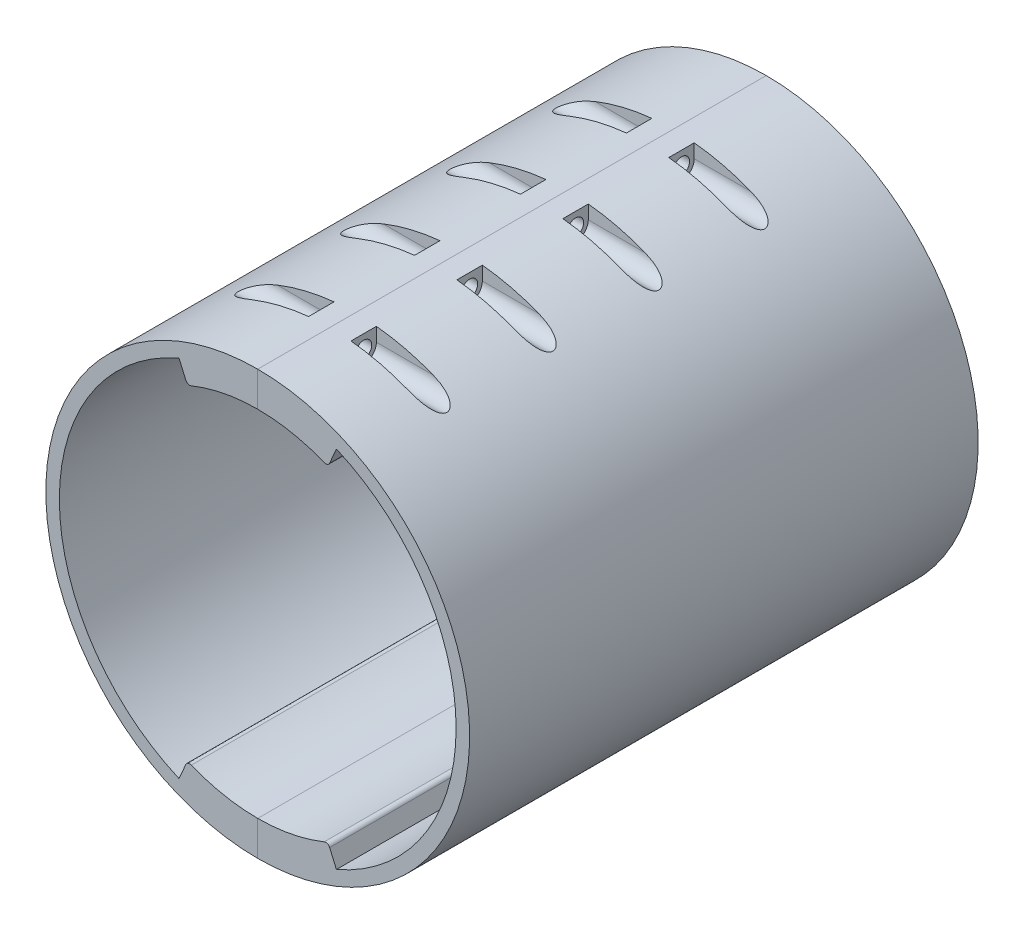
SolidWorks part; units mm, degrees
material "ABS"
ref_plane "Front Plane" through (0, 0, 0) normal (0, 0, 1) x (1, 0, 0)
ref_plane "Top Plane" through (0, 0, 0) normal (0, 1, 0) x (1, 0, 0)
ref_plane "Right Plane" through (0, 0, 0) normal (1, 0, 0) x (0, 0, -1)
sketch "Sketch1" plane through (0, 0, 0) normal (0, 1, 0) x (1, 0, 0)
  line L1 (0, 0) -> (-300, 0)
  line L2 (0, 0) -> (0, -170)
  line L3 (0, -170) -> (-300, -170)
  line L4 (-300, 0) -> (-300, -170)
  dimension "D1" = 300
  dimension "D2" = 170
extrude "Boss-Extrude1" add sketch "Sketch1" along normal blind 225
shell "Shell1" thickness 10
sketch "Sketch2" plane through (0, 0, 10) normal (0, 0, 1) x (1, 0, 0)
  line L0 (-290, 112.5) -> (-10, 112.5) construction
  line L1 (-290, 215) -> (-290, 10) construction
  line L2 (-10, 215) -> (-10, 10) construction
  circle A0 centre (-150, 112.5) radius 6.5
  dimension "D1" = 13
  dimension "D2" = 140
extrude "Cut-Extrude1" cut sketch "Sketch2" against normal blind 10
sketch "Sketch3" plane through (0, 0, 10) normal (0, 0, 1) x (1, 0, 0)
  line L0 (-150, 112.5) -> (-150, 135) construction
  line L1 (-150, 112.5) -> (-134.0901, 128.4099) construction
  circle A0 centre (-150, 112.5) radius 22.5 construction
  dimension "D1" = 45
  dimension "D2" = 45
hole_wizard "M5 Clearance Hole1" positions "Sketch4" profile "Sketch5" hole size "M5" standard "ANSI Metric"
sketch "Sketch4" plane through (0, 0, 10) normal (0, 0, 1) x (1, 0, 0)
  point P0 (-134.0901, 128.4099)
sketch "Sketch5" plane through (-134.0901, 128.4099, 10) normal (1, 0, 0) x (0, -1, 0)
  line L0 (0, 0) -> (0, 21.6524)
  line L1 (0, 21.6524) -> (2.75, 20)
  line L2 (2.75, 20) -> (2.75, 0.025)
  line L3 (2.75, 0.025) -> (2.775, 0)
  line L5 (2.775, 0) -> (0, 0)
  line L6 (-2.75, 0.025) -> (-2.775, 0) construction
  line L10 (0, 21.6524) -> (-2.75, 20) construction
  line L11 (0, -6.35) -> (0, 107.95) construction
  dimension "Hole Dia." = 5.5
  dimension "Hole Depth" = 20
  dimension "Near C'Sink Dia." = 5.55
  dimension "Near C'Sink Angle" = 90
  dimension "Drill Angle" = 118
pattern_circular "CirPattern1" count 4 over 360 about axis through (-150, 112.5, 0) along (0, 0, 1) of "M5 Clearance Hole1"
sketch "Sketch6" plane through (0, 0, 0) normal (0, 0, -1) x (-1, 0, 0)
  circle A0 centre (150, 112.5) radius 100
  dimension "D1" = 200
extrude "Cut-Extrude2" cut sketch "Sketch6" against normal through all flip side to cut
sketch "Sketch7" plane through (0, 0, 10) normal (0, 0, 1) x (1, 0, 0)
  circle A0 centre (-150, 112.5) radius 93.619
  circle A2 centre (-150, 112.5) radius 100
  dimension "D1" = 6.381
extrude "Boss-Extrude2" add sketch "Sketch7" along normal blind 200
sketch "Sketch8" plane through (0, 0, 0) normal (0, 0, -1) x (-1, 0, 0)
  circle A0 centre (150, 112.5) radius 95
  circle A1 centre (150, 112.5) radius 100
  circle A2 centre (150, 112.5) radius 100 construction
  dimension "D1" = 5
extrude "Boss-Extrude3" add sketch "Sketch8" along normal blind 30
ref_plane "Plane1" through (-50, 0, 0) normal (1, 0, 0) x (0, 0, -1)
ref_plane "Plane2" through (-150, 0, 0) normal (1, 0, 0) x (0, 0, -1)
sketch "Sketch11" plane through (0, 0, 0) normal (0, 0, -1) x (-1, 0, 0)
  circle A0 centre (150, 112.5) radius 90
  circle A1 centre (150, 112.5) radius 95
  circle A2 centre (150, 112.5) radius 95 construction
  dimension "D1" = 180
extrude "Boss-Extrude4" add sketch "Sketch11" along normal up to surface (30 mm away) up to face at (-250, 112.5, -30)
sketch "Sketch12" plane through (-150, 0, 0) normal (1, 0, 0) x (0, 0, -1)
  line L0 (-170, 205.5) -> (30, 205.5) construction
  line L1 (30, 12.5) -> (30, 212.5) construction
  line L2 (-210, 212.5) -> (-210, 12.5) construction
  line L3 (30, 212.5) -> (-210, 212.5) construction
  line L4 (-176, 205.5) -> (-176, 212.5)
  line L5 (-164, 205.5) -> (-164, 212.5)
  line L6 (-164, 212.5) -> (-176, 212.5)
  line L7 (-126, 205.5) -> (-126, 212.5)
  line L8 (-114, 212.5) -> (-126, 212.5)
  line L9 (-114, 205.5) -> (-114, 212.5)
  line L10 (-76, 205.5) -> (-76, 212.5)
  line L11 (-64, 212.5) -> (-76, 212.5)
  line L12 (-64, 205.5) -> (-64, 212.5)
  line L13 (-26, 205.5) -> (-26, 212.5)
  line L14 (-14, 212.5) -> (-26, 212.5)
  line L15 (-14, 205.5) -> (-14, 212.5)
  line L16 (-210, 112.5) -> (30, 112.5) construction
  line L17 (-170, 19.5) -> (30, 19.5) construction
  line L18 (-14, 19.5) -> (-14, 12.5)
  line L19 (-14, 12.5) -> (-26, 12.5)
  line L20 (-26, 19.5) -> (-26, 12.5)
  line L21 (-64, 19.5) -> (-64, 12.5)
  line L22 (-64, 12.5) -> (-76, 12.5)
  line L23 (-76, 19.5) -> (-76, 12.5)
  line L24 (-114, 19.5) -> (-114, 12.5)
  line L25 (-114, 12.5) -> (-126, 12.5)
  line L26 (-126, 19.5) -> (-126, 12.5)
  line L27 (-164, 12.5) -> (-176, 12.5)
  line L28 (-164, 19.5) -> (-164, 12.5)
  line L29 (-176, 19.5) -> (-176, 12.5)
  arc A0 (-176, 205.5) -> (-164, 205.5) centre (-170, 205.5) ccw
  arc A1 (-126, 205.5) -> (-114, 205.5) centre (-120, 205.5) ccw
  arc A2 (-76, 205.5) -> (-64, 205.5) centre (-70, 205.5) ccw
  arc A3 (-26, 205.5) -> (-14, 205.5) centre (-20, 205.5) ccw
  arc A4 (-26, 19.5) -> (-14, 19.5) centre (-20, 19.5) cw
  arc A5 (-76, 19.5) -> (-64, 19.5) centre (-70, 19.5) cw
  arc A6 (-126, 19.5) -> (-114, 19.5) centre (-120, 19.5) cw
  arc A7 (-176, 19.5) -> (-164, 19.5) centre (-170, 19.5) cw
  dimension "D2" = 12
  dimension "D1" = 40
  dimension "D3" = 7
  dimension "D4" = 4
ref_plane "Plane3" through (-140, 0, 0) normal (1, 0, 0) x (0, 0, -1)
sketch "Sketch13" plane through (-140, 0, 0) normal (1, 0, 0) x (0, 0, -1)
  line L3 (-176, 212.5) -> (-176, 205.5)
  line L4 (-164, 212.5) -> (-176, 212.5)
  line L5 (-164, 205.5) -> (-164, 212.5)
  line L6 (-176, 212.5) -> (-176, 205.5)
  line L7 (-164, 212.5) -> (-176, 212.5)
  line L8 (-164, 205.5) -> (-164, 212.5)
  line L9 (-26, 212.5) -> (-26, 205.5)
  line L10 (-14, 212.5) -> (-26, 212.5)
  line L11 (-14, 205.5) -> (-14, 212.5)
  line L12 (-26, 212.5) -> (-26, 205.5)
  line L13 (-14, 212.5) -> (-26, 212.5)
  line L14 (-14, 205.5) -> (-14, 212.5)
  line L15 (-76, 212.5) -> (-76, 205.5)
  line L16 (-64, 212.5) -> (-76, 212.5)
  line L17 (-64, 205.5) -> (-64, 212.5)
  line L18 (-76, 212.5) -> (-76, 205.5)
  line L19 (-64, 212.5) -> (-76, 212.5)
  line L20 (-64, 205.5) -> (-64, 212.5)
  line L21 (-114, 212.5) -> (-126, 212.5)
  line L22 (-114, 205.5) -> (-114, 212.5)
  line L23 (-126, 212.5) -> (-126, 205.5)
  line L24 (-114, 212.5) -> (-126, 212.5)
  line L25 (-114, 205.5) -> (-114, 212.5)
  line L26 (-126, 212.5) -> (-126, 205.5)
  line L27 (-114, 12.5) -> (-114, 19.5)
  line L28 (-126, 12.5) -> (-114, 12.5)
  line L29 (-126, 19.5) -> (-126, 12.5)
  line L30 (-114, 12.5) -> (-114, 19.5)
  line L31 (-126, 12.5) -> (-114, 12.5)
  line L32 (-126, 19.5) -> (-126, 12.5)
  line L33 (-64, 12.5) -> (-64, 19.5)
  line L34 (-76, 12.5) -> (-64, 12.5)
  line L35 (-76, 19.5) -> (-76, 12.5)
  line L36 (-64, 12.5) -> (-64, 19.5)
  line L37 (-76, 12.5) -> (-64, 12.5)
  line L38 (-76, 19.5) -> (-76, 12.5)
  line L39 (-14, 12.5) -> (-14, 19.5)
  line L40 (-26, 12.5) -> (-14, 12.5)
  line L41 (-26, 19.5) -> (-26, 12.5)
  line L42 (-14, 12.5) -> (-14, 19.5)
  line L43 (-26, 12.5) -> (-14, 12.5)
  line L44 (-26, 19.5) -> (-26, 12.5)
  line L45 (-176, 12.5) -> (-164, 12.5)
  line L46 (-176, 19.5) -> (-176, 12.5)
  line L47 (-164, 12.5) -> (-164, 19.5)
  line L48 (-176, 12.5) -> (-164, 12.5)
  line L49 (-176, 19.5) -> (-176, 12.5)
  line L50 (-164, 12.5) -> (-164, 19.5)
  arc A1 (-176, 205.5) -> (-164, 205.5) centre (-170, 205.5) ccw
  arc A2 (-176, 205.5) -> (-164, 205.5) centre (-170, 205.5) ccw
  arc A3 (-26, 205.5) -> (-14, 205.5) centre (-20, 205.5) ccw
  arc A4 (-26, 205.5) -> (-14, 205.5) centre (-20, 205.5) ccw
  arc A5 (-76, 205.5) -> (-64, 205.5) centre (-70, 205.5) ccw
  arc A6 (-76, 205.5) -> (-64, 205.5) centre (-70, 205.5) ccw
  arc A7 (-126, 205.5) -> (-114, 205.5) centre (-120, 205.5) ccw
  arc A8 (-126, 205.5) -> (-114, 205.5) centre (-120, 205.5) ccw
  arc A9 (-114, 19.5) -> (-126, 19.5) centre (-120, 19.5) ccw
  arc A10 (-114, 19.5) -> (-126, 19.5) centre (-120, 19.5) ccw
  arc A11 (-64, 19.5) -> (-76, 19.5) centre (-70, 19.5) ccw
  arc A12 (-64, 19.5) -> (-76, 19.5) centre (-70, 19.5) ccw
  arc A13 (-14, 19.5) -> (-26, 19.5) centre (-20, 19.5) ccw
  arc A14 (-14, 19.5) -> (-26, 19.5) centre (-20, 19.5) ccw
  arc A15 (-164, 19.5) -> (-176, 19.5) centre (-170, 19.5) ccw
  arc A16 (-164, 19.5) -> (-176, 19.5) centre (-170, 19.5) ccw
  dimension "D1" = 0
  dimension "D2" = 0
  dimension "D3" = 0
  dimension "D4" = 0
  dimension "D5" = 0
  dimension "D6" = 0
  dimension "D7" = 0
  dimension "D8" = 0
extrude "Cut-Extrude3" cut sketch "Sketch13" along normal blind 47
mirror "Mirror1" about plane through (-150, 0, 0) normal (1, 0, 0) of "Cut-Extrude3"
sketch "Sketch15" plane through (0, 0, 210) normal (0, 0, 1) x (1, 0, 0)
  line L0 (-150, 12.5) -> (-150, 212.5) construction
  line L1 (-187.1354, 198.4388) -> (-183.1688, 189.2592)
  line L2 (-112.8646, 198.4388) -> (-116.8312, 189.2592)
  line L3 (-150, 112.5) -> (-86.3141, 112.5) construction
  line L4 (-112.8646, 26.5612) -> (-116.8312, 35.7408)
  line L5 (-187.1354, 26.5612) -> (-183.1688, 35.7408)
  circle A0 centre (-150, 112.5) radius 100 construction
  arc A1 (-187.1354, 198.4388) -> (-112.8646, 198.4388) centre (-150, 112.5) cw
  circle A2 centre (-150, 112.5) radius 93.619 construction
  arc A3 (-183.1688, 189.2592) -> (-116.8312, 189.2592) centre (-150, 112.5) cw
  arc A4 (-183.1688, 35.7408) -> (-116.8312, 35.7408) centre (-150, 112.5) ccw
  arc A5 (-187.1354, 26.5612) -> (-112.8646, 26.5612) centre (-150, 112.5) ccw
  point P7 (-150, 112.5)
  dimension "D1" = 10
extrude "Boss-Extrude6" add sketch "Sketch15" against normal up to next
fillet "Fillet2" radius 2 4 edges at (-116.8312, 189.2592, 110) (-183.1688, 189.2592, 110) (-183.1688, 35.7408, 110) (-116.8312, 35.7408, 110)
sketch "Sketch16" plane through (-140, 0, 0) normal (1, 0, 0) x (0, 0, -1)
  line L3 (-76, 212.5) -> (-76, 205.5)
  line L4 (-64, 205.5) -> (-64, 212.5)
  line L5 (-64, 212.5) -> (-76, 212.5)
  line L6 (-76, 212.5) -> (-76, 205.5)
  line L7 (-64, 205.5) -> (-64, 212.5)
  line L8 (-64, 212.5) -> (-76, 212.5)
  line L9 (-26, 212.5) -> (-26, 205.5)
  line L10 (-14, 205.5) -> (-14, 212.5)
  line L11 (-14, 212.5) -> (-26, 212.5)
  line L12 (-26, 212.5) -> (-26, 205.5)
  line L13 (-14, 205.5) -> (-14, 212.5)
  line L14 (-14, 212.5) -> (-26, 212.5)
  line L15 (-176, 212.5) -> (-176, 205.5)
  line L16 (-164, 205.5) -> (-164, 212.5)
  line L17 (-164, 212.5) -> (-176, 212.5)
  line L18 (-176, 212.5) -> (-176, 205.5)
  line L19 (-164, 205.5) -> (-164, 212.5)
  line L20 (-164, 212.5) -> (-176, 212.5)
  line L21 (-64, 12.5) -> (-64, 19.5)
  line L22 (-76, 19.5) -> (-76, 12.5)
  line L23 (-76, 12.5) -> (-64, 12.5)
  line L24 (-64, 12.5) -> (-64, 19.5)
  line L25 (-76, 19.5) -> (-76, 12.5)
  line L26 (-76, 12.5) -> (-64, 12.5)
  line L27 (-114, 12.5) -> (-114, 19.5)
  line L28 (-126, 19.5) -> (-126, 12.5)
  line L29 (-126, 12.5) -> (-114, 12.5)
  line L30 (-114, 12.5) -> (-114, 19.5)
  line L31 (-126, 19.5) -> (-126, 12.5)
  line L32 (-126, 12.5) -> (-114, 12.5)
  line L33 (-114, 212.5) -> (-126, 212.5)
  line L34 (-114, 205.5) -> (-114, 212.5)
  line L35 (-126, 212.5) -> (-126, 205.5)
  line L36 (-114, 212.5) -> (-126, 212.5)
  line L37 (-114, 205.5) -> (-114, 212.5)
  line L38 (-126, 212.5) -> (-126, 205.5)
  line L39 (-176, 12.5) -> (-164, 12.5)
  line L40 (-164, 12.5) -> (-164, 19.5)
  line L41 (-176, 19.5) -> (-176, 12.5)
  line L42 (-176, 12.5) -> (-164, 12.5)
  line L43 (-164, 12.5) -> (-164, 19.5)
  line L44 (-176, 19.5) -> (-176, 12.5)
  line L45 (-26, 19.5) -> (-26, 12.5)
  line L46 (-14, 12.5) -> (-14, 19.5)
  line L47 (-26, 12.5) -> (-14, 12.5)
  line L48 (-26, 19.5) -> (-26, 12.5)
  line L49 (-14, 12.5) -> (-14, 19.5)
  line L50 (-26, 12.5) -> (-14, 12.5)
  arc A1 (-76, 205.5) -> (-64, 205.5) centre (-70, 205.5) ccw
  arc A2 (-76, 205.5) -> (-64, 205.5) centre (-70, 205.5) ccw
  arc A3 (-26, 205.5) -> (-14, 205.5) centre (-20, 205.5) ccw
  arc A4 (-26, 205.5) -> (-14, 205.5) centre (-20, 205.5) ccw
  arc A5 (-176, 205.5) -> (-164, 205.5) centre (-170, 205.5) ccw
  arc A6 (-176, 205.5) -> (-164, 205.5) centre (-170, 205.5) ccw
  arc A7 (-64, 19.5) -> (-76, 19.5) centre (-70, 19.5) ccw
  arc A8 (-64, 19.5) -> (-76, 19.5) centre (-70, 19.5) ccw
  arc A9 (-114, 19.5) -> (-126, 19.5) centre (-120, 19.5) ccw
  arc A10 (-114, 19.5) -> (-126, 19.5) centre (-120, 19.5) ccw
  arc A11 (-126, 205.5) -> (-114, 205.5) centre (-120, 205.5) ccw
  arc A12 (-126, 205.5) -> (-114, 205.5) centre (-120, 205.5) ccw
  arc A13 (-164, 19.5) -> (-176, 19.5) centre (-170, 19.5) ccw
  arc A14 (-164, 19.5) -> (-176, 19.5) centre (-170, 19.5) ccw
  arc A15 (-14, 19.5) -> (-26, 19.5) centre (-20, 19.5) ccw
  arc A16 (-14, 19.5) -> (-26, 19.5) centre (-20, 19.5) ccw
  dimension "D1" = 0
  dimension "D2" = 0
  dimension "D3" = 0
  dimension "D4" = 0
  dimension "D5" = 0
  dimension "D6" = 0
  dimension "D7" = 0
  dimension "D8" = 0
extrude "Cut-Extrude4" cut sketch "Sketch16" along normal blind 35
sketch "Sketch17" plane through (-160, 0, 0) normal (-1, 0, 0) x (0, 0, 1)
  line L3 (76, 205.5) -> (76, 212.5)
  line L4 (64, 212.5) -> (64, 205.5)
  line L5 (76, 212.5) -> (64, 212.5)
  line L6 (76, 205.5) -> (76, 212.5)
  line L7 (64, 212.5) -> (64, 205.5)
  line L8 (76, 212.5) -> (64, 212.5)
  line L9 (26, 205.5) -> (26, 212.5)
  line L10 (14, 212.5) -> (14, 205.5)
  line L11 (26, 212.5) -> (14, 212.5)
  line L12 (26, 205.5) -> (26, 212.5)
  line L13 (14, 212.5) -> (14, 205.5)
  line L14 (26, 212.5) -> (14, 212.5)
  line L15 (176, 205.5) -> (176, 212.5)
  line L16 (164, 212.5) -> (164, 205.5)
  line L17 (176, 212.5) -> (164, 212.5)
  line L18 (176, 205.5) -> (176, 212.5)
  line L19 (164, 212.5) -> (164, 205.5)
  line L20 (176, 212.5) -> (164, 212.5)
  line L21 (64, 19.5) -> (64, 12.5)
  line L22 (76, 12.5) -> (76, 19.5)
  line L23 (64, 12.5) -> (76, 12.5)
  line L24 (64, 19.5) -> (64, 12.5)
  line L25 (76, 12.5) -> (76, 19.5)
  line L26 (64, 12.5) -> (76, 12.5)
  line L27 (114, 19.5) -> (114, 12.5)
  line L28 (126, 12.5) -> (126, 19.5)
  line L29 (114, 12.5) -> (126, 12.5)
  line L30 (114, 19.5) -> (114, 12.5)
  line L31 (126, 12.5) -> (126, 19.5)
  line L32 (114, 12.5) -> (126, 12.5)
  line L33 (126, 212.5) -> (114, 212.5)
  line L34 (114, 212.5) -> (114, 205.5)
  line L35 (126, 205.5) -> (126, 212.5)
  line L36 (126, 212.5) -> (114, 212.5)
  line L37 (114, 212.5) -> (114, 205.5)
  line L38 (126, 205.5) -> (126, 212.5)
  line L39 (164, 12.5) -> (176, 12.5)
  line L40 (164, 19.5) -> (164, 12.5)
  line L41 (176, 12.5) -> (176, 19.5)
  line L42 (164, 12.5) -> (176, 12.5)
  line L43 (164, 19.5) -> (164, 12.5)
  line L44 (176, 12.5) -> (176, 19.5)
  line L45 (26, 12.5) -> (26, 19.5)
  line L46 (14, 19.5) -> (14, 12.5)
  line L47 (14, 12.5) -> (26, 12.5)
  line L48 (26, 12.5) -> (26, 19.5)
  line L49 (14, 19.5) -> (14, 12.5)
  line L50 (14, 12.5) -> (26, 12.5)
  arc A1 (64, 205.5) -> (76, 205.5) centre (70, 205.5) ccw
  arc A2 (64, 205.5) -> (76, 205.5) centre (70, 205.5) ccw
  arc A3 (14, 205.5) -> (26, 205.5) centre (20, 205.5) ccw
  arc A4 (14, 205.5) -> (26, 205.5) centre (20, 205.5) ccw
  arc A5 (164, 205.5) -> (176, 205.5) centre (170, 205.5) ccw
  arc A6 (164, 205.5) -> (176, 205.5) centre (170, 205.5) ccw
  arc A7 (76, 19.5) -> (64, 19.5) centre (70, 19.5) ccw
  arc A8 (76, 19.5) -> (64, 19.5) centre (70, 19.5) ccw
  arc A9 (126, 19.5) -> (114, 19.5) centre (120, 19.5) ccw
  arc A10 (126, 19.5) -> (114, 19.5) centre (120, 19.5) ccw
  arc A11 (114, 205.5) -> (126, 205.5) centre (120, 205.5) ccw
  arc A12 (114, 205.5) -> (126, 205.5) centre (120, 205.5) ccw
  arc A13 (176, 19.5) -> (164, 19.5) centre (170, 19.5) ccw
  arc A14 (176, 19.5) -> (164, 19.5) centre (170, 19.5) ccw
  arc A15 (26, 19.5) -> (14, 19.5) centre (20, 19.5) ccw
  arc A16 (26, 19.5) -> (14, 19.5) centre (20, 19.5) ccw
  dimension "D1" = 0
  dimension "D2" = 0
  dimension "D3" = 0
  dimension "D4" = 0
  dimension "D5" = 0
  dimension "D6" = 0
  dimension "D7" = 0
  dimension "D8" = 0
extrude "Cut-Extrude5" cut sketch "Sketch17" along normal blind 35
hole_wizard "M7 Clearance Hole1" positions "3DSketch1" profile "Sketch18" hole size "M7" standard "ANSI Metric" end condition through all
sketch3d "3DSketch1"
  line L0 (-188.7844, 205.5, 20) -> (-163.1072, 205.5, 20) construction
  line L1 (-188.7844, 205.5, 70) -> (-163.1072, 205.5, 70) construction
  line L2 (-188.7844, 205.5, 120) -> (-163.1072, 205.5, 120) construction
  line L3 (-188.777, 19.5, 20) -> (-163.1071, 19.5, 20) construction
  line L4 (-188.777, 19.5, 70) -> (-163.1071, 19.5, 70) construction
  line L5 (-188.777, 19.5, 120) -> (-163.1071, 19.5, 120) construction
  line L6 (-188.7844, 19.5, 170) -> (-163.1072, 19.5, 170) construction
  line L7 (-188.7844, 205.5, 170) -> (-163.1072, 205.5, 170) construction
  point P0 (-160, 205.5, 20)
  point P4 (-160, 205.5, 70)
  point P8 (-160, 205.5, 120)
  point P12 (-160, 19.5, 20)
  point P16 (-160, 19.5, 70)
  point P20 (-160, 19.5, 120)
  point P24 (-160, 19.5, 170)
  point P28 (-160, 205.5, 170)
sketch "Sketch18" plane through (-160, 205.5, 20) normal (0, 1, 0) x (0, 0, 1)
  line L0 (0, 0) -> (0, 110)
  line L1 (0, 110) -> (3.8, 110)
  line L2 (3.8, 110) -> (3.8, 0.025)
  line L3 (3.8, 0.025) -> (3.825, 0)
  line L5 (3.825, 0) -> (0, 0)
  line L6 (-3.8, 0.025) -> (-3.825, 0) construction
  line L11 (0, -6.35) -> (0, 107.95) construction
  dimension "Thru Hole Dia." = 7.6
  dimension "Thru Hole Depth" = 110
  dimension "Near C'Sink Dia." = 7.65
  dimension "Near C'Sink Angle" = 90
split "Split1" trim tools "Plane2" bodies to split 119 resulting bodies 120 121
